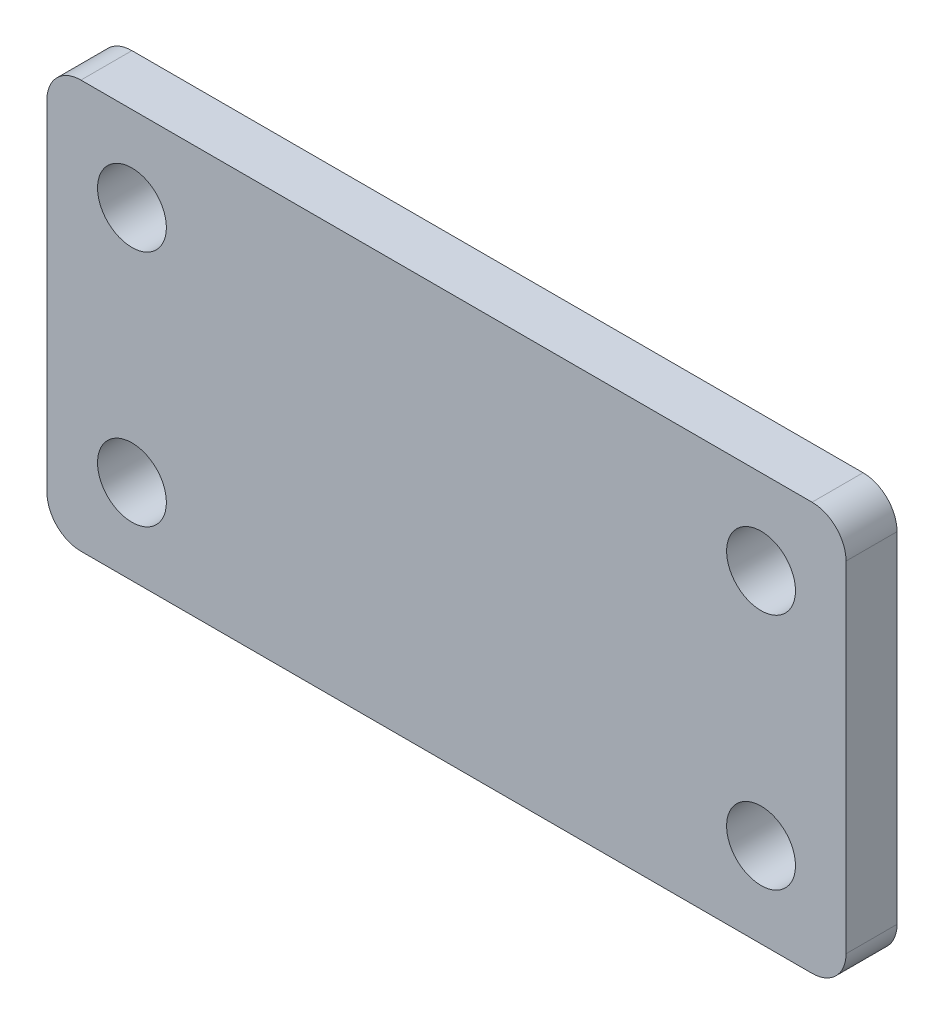
SolidWorks part; units mm, degrees
material "POM Acetal Coopolymer聚甲醛树脂"
ref_plane "前视基准面" through (0, 0, 0) normal (0, 0, 1) x (1, 0, 0)
ref_plane "上视基准面" through (0, 0, 0) normal (0, 1, 0) x (1, 0, 0)
ref_plane "右视基准面" through (0, 0, 0) normal (1, 0, 0) x (0, 0, -1)
sketch "草图1" plane through (0, 0, 0) normal (0, 0, 1) x (1, 0, 0)
  line L1 (-18.5, -7) -> (18.5, -7) construction
  line L2 (-18.5, -7) -> (-18.5, 7) construction
  line L3 (-18.5, 7) -> (18.5, 7) construction
  line L4 (18.5, -7) -> (18.5, 7) construction
  line L5 (0, 7) -> (0, -7) construction
  line L6 (-18.5, 0) -> (18.5, 0) construction
  line L7 (-23.5, -12) -> (23.5, -12)
  line L8 (-23.5, -12) -> (-23.5, 12)
  line L9 (-23.5, 12) -> (23.5, 12)
  line L10 (23.5, -12) -> (23.5, 12)
  line L11 (0, 12) -> (0, -12) construction
  line L12 (-23.5, 0) -> (23.5, 0) construction
  circle A0 centre (18.5, 7) radius 2.025
  circle A1 centre (-18.5, 7) radius 2.025
  circle A2 centre (-18.5, -7) radius 2.025
  circle A3 centre (18.5, -7) radius 2.025
  point P0 (0, 0)
  point P8 (0, 0)
  dimension "D3" = 4.05
  dimension "D1" = 14
  dimension "D2" = 37
  dimension "D4" = 5
  dimension "D5" = 5
extrude "凸台-拉伸1" add sketch "草图1" along normal blind 3
fillet "圆角1" radius 2 4 edges at (23.5, -12, 1.5) (-23.5, -12, 1.5) (-23.5, 12, 1.5) (23.5, 12, 1.5)
equation "\"D4@草图1\"=\"D5@草图1\""
